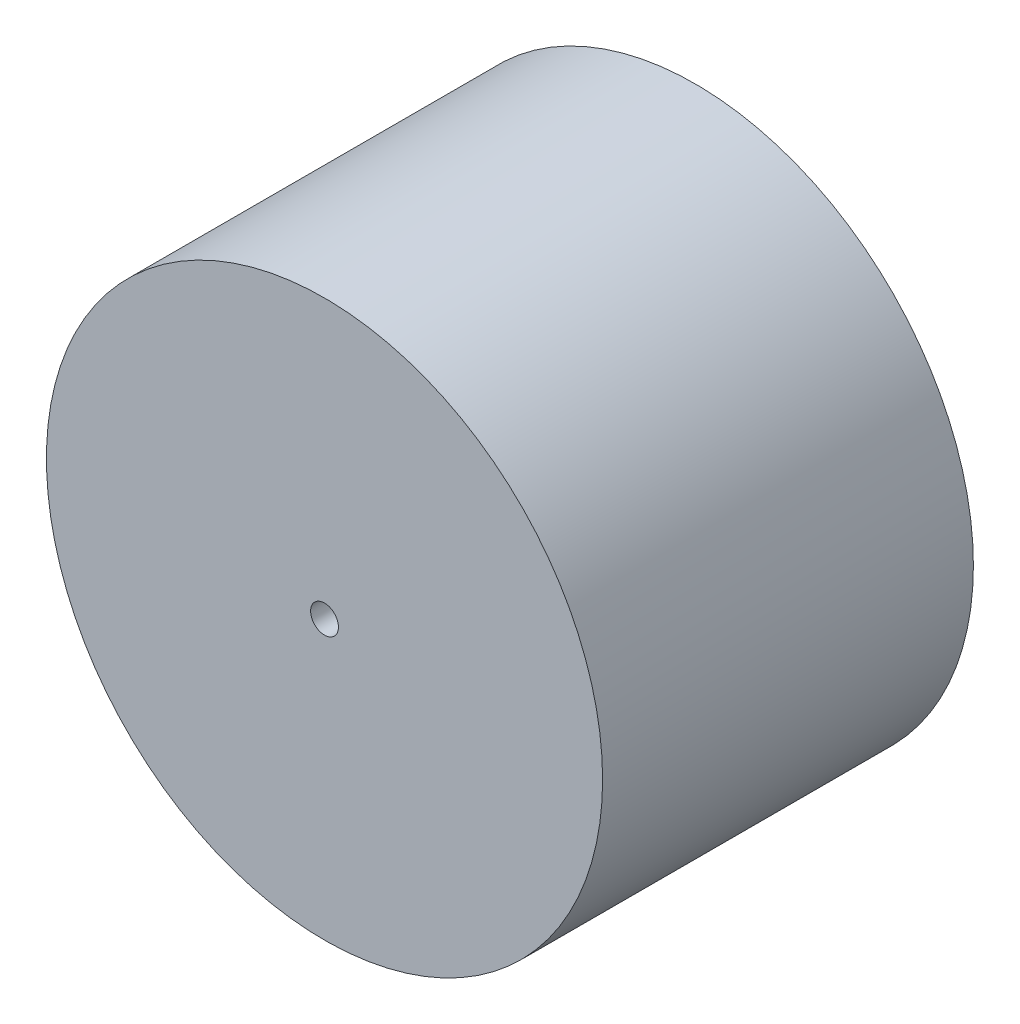
SolidWorks part; units mm, degrees
ref_plane "Front Plane" through (0, 0, 0) normal (0, 0, 1) x (1, 0, 0)
ref_plane "Top Plane" through (0, 0, 0) normal (0, 1, 0) x (1, 0, 0)
ref_plane "Right Plane" through (0, 0, 0) normal (1, 0, 0) x (0, 0, -1)
sketch "Sketch1" plane through (0, 0, 0) normal (0, 0, 1) x (1, 0, 0)
  circle A0 centre (0, 0) radius 30
  dimension "D1" = 60
extrude "Boss-Extrude1" add sketch "Sketch1" along normal blind 40
sketch "Sketch2" plane through (0, 0, 0) normal (0, 0, -1) x (-1, 0, 0)
  circle A0 centre (0, 0) radius 20
  dimension "D1" = 40
extrude "Cut-Extrude1" cut sketch "Sketch2" against normal blind 25
sketch "Sketch3" plane through (0, 0, 25) normal (0, 0, -1) x (-1, 0, 0)
  line L1 (4.0828, -4.3967) -> (5.849, 1.3374)
  line L2 (5.849, 1.3374) -> (1.7663, 5.7341)
  line L3 (1.7663, 5.7341) -> (-4.0828, 4.3967)
  line L4 (-4.0828, 4.3967) -> (-5.849, -1.3374)
  line L5 (-5.849, -1.3374) -> (-1.7663, -5.7341)
  line L6 (-1.7663, -5.7341) -> (4.0828, -4.3967)
  circle A0 centre (0, 0) radius 5.1962 construction
  dimension "D1" = 6
extrude "Cut-Extrude2" cut sketch "Sketch3" against normal blind 5
sketch "Sketch5" plane through (0, 0, 40) normal (0, 0, 1) x (1, 0, 0)
  circle A0 centre (0, 0) radius 1.5
  dimension "D1" = 3
extrude "Cut-Extrude3" cut sketch "Sketch5" against normal blind 40
